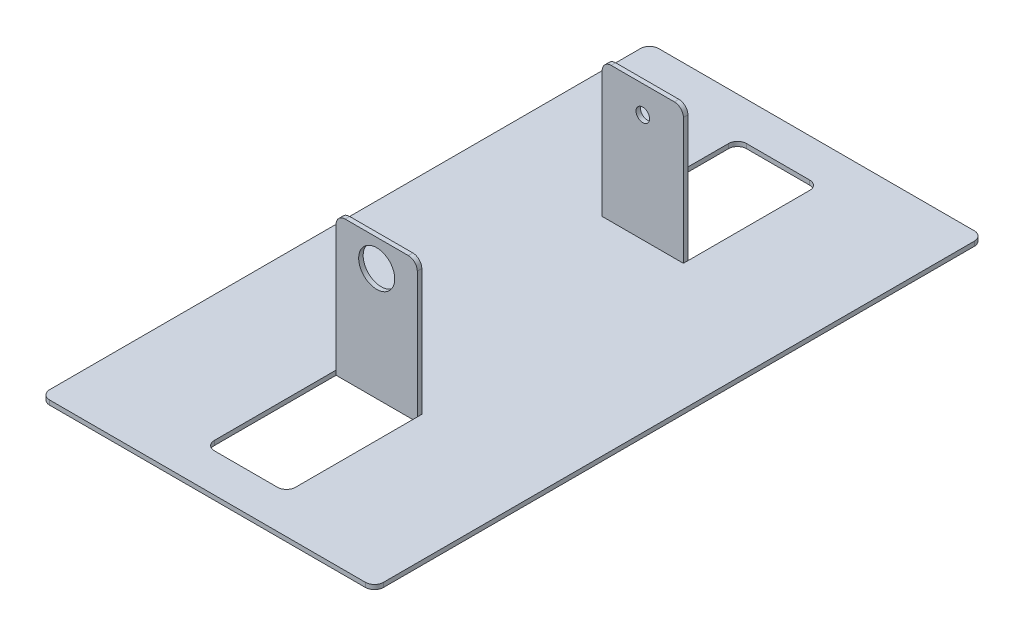
SolidWorks part; units mm, degrees
ref_plane "Front Plane" through (0, 0, 0) normal (0, 0, 1) x (1, 0, 0)
ref_plane "Top Plane" through (0, 0, 0) normal (0, 1, 0) x (1, 0, 0)
ref_plane "Right Plane" through (0, 0, 0) normal (1, 0, 0) x (0, 0, -1)
sketch "Sketch1" plane through (0, 0, 0) normal (0, 1, 0) x (1, 0, 0)
  line L0 (-37, 0) -> (37, 0) construction
  line L1 (-37, -67.5) -> (37, -67.5)
  line L2 (-37, -67.5) -> (-37, 67.5)
  line L3 (-37, 67.5) -> (37, 67.5)
  line L4 (37, -67.5) -> (37, 67.5)
  line L5 (-37, -67.5) -> (37, 67.5) construction
  line L6 (-37, 67.5) -> (37, -67.5) construction
  line L7 (-9, -59) -> (9, -29) construction
  line L8 (-9, 29) -> (9, 29)
  line L9 (-9, 29) -> (-9, 59)
  line L10 (-9, 59) -> (9, 59)
  line L11 (9, 29) -> (9, 59)
  line L12 (-9, 29) -> (9, 59) construction
  line L13 (-9, 59) -> (9, 29) construction
  line L14 (-9, -29) -> (9, -59) construction
  line L15 (9, -29) -> (9, -59)
  line L16 (-9, -59) -> (9, -59)
  line L17 (-9, -29) -> (-9, -59)
  line L18 (-9, -29) -> (9, -29)
  point P0 (0, 0)
  point P8 (0, 44)
  point P17 (0, -44)
  dimension "D1" = 74
  dimension "D2" = 135
  dimension "D3" = 18
  dimension "D4" = 30
  dimension "D5" = 58
extrude "Boss-Extrude1" add sketch "Sketch1" along normal blind 1
sketch "Sketch2" plane through (0, 1, 0) normal (0, 1, 0) x (1, 0, 0)
  line L0 (-37, 0) -> (37, 0) construction
  line L1 (-9, 29) -> (9, 29)
  line L2 (-9, 29) -> (-9, 30)
  line L3 (-9, 30) -> (9, 30)
  line L4 (9, 29) -> (9, 30)
  line L5 (-37, 67.5) -> (-37, -67.5) construction
  line L6 (37, -67.5) -> (37, 67.5) construction
  line L7 (9, -29) -> (9, -30)
  line L8 (-9, -30) -> (9, -30)
  line L9 (-9, -29) -> (-9, -30)
  line L10 (-9, -29) -> (9, -29)
  line L11 (9, 29) -> (9, 59) construction
  dimension "D1" = 1
extrude "Boss-Extrude2" add sketch "Sketch2" along normal blind 31 from offset 1 offset against normal yes
sketch "Sketch5" plane through (0, 0, 30) normal (0, 0, 1) x (1, 0, 0)
  line L0 (-9, 31) -> (9, 31) construction
  circle A0 centre (0, 25) radius 4
  dimension "D1" = 8
  dimension "D2" = 6
extrude "Cut-Extrude3" cut sketch "Sketch5" against normal up to next
sketch "Sketch6" plane through (0, 0, -29) normal (0, 0, 1) x (1, 0, 0)
  circle A0 centre (0, 25) radius 1.5
  dimension "D1" = 3
extrude "Cut-Extrude4" cut sketch "Sketch6" against normal up to next
fillet "Fillet2" radius 2 12 edges at (-9, 0.5, 59) (9, 0.5, 59) (-9, 31, 29.5) (9, 31, 29.5) (9, 31, -29.5) (-9, 31, -29.5) (9, 0.5, -59) (-9, 0.5, -59) (-37, 0.5, -67.5) (37, 0.5, -67.5) (37, 0.5, 67.5) (-37, 0.5, 67.5)
